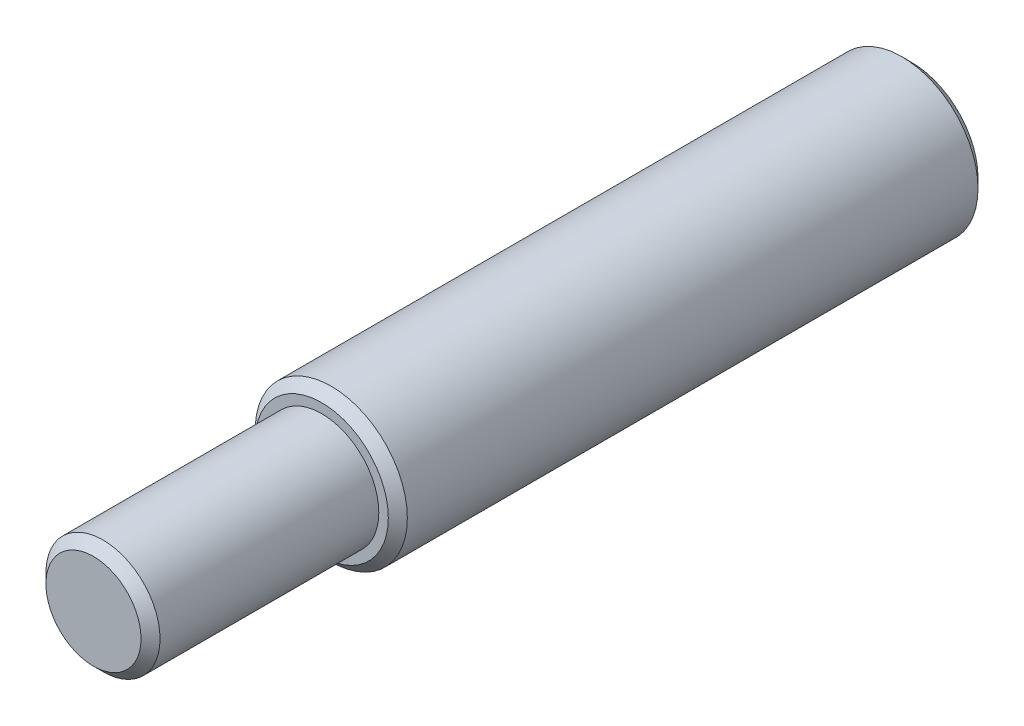
SolidWorks part; units mm, degrees
ref_plane "前视基准面" through (0, 0, 0) normal (0, 0, 1) x (1, 0, 0)
ref_plane "上视基准面" through (0, 0, 0) normal (0, 1, 0) x (1, 0, 0)
ref_plane "右视基准面" through (0, 0, 0) normal (1, 0, 0) x (0, 0, -1)
sketch "草图1" plane through (0, 0, 0) normal (0, 0, 1) x (1, 0, 0)
  circle A0 centre (0, 0) radius 4
  dimension "D1" = 8
extrude "凸台-拉伸1" add sketch "草图1" along normal blind 10
sketch "草图2" plane through (0, 0, 10) normal (0, 0, 1) x (1, 0, 0)
  line L1 (10, 0) -> (5, 8.6603)
  line L2 (5, 8.6603) -> (-5, 8.6603)
  line L3 (-5, 8.6603) -> (-10, 0)
  line L4 (-10, 0) -> (-5, -8.6603)
  line L5 (-5, -8.6603) -> (5, -8.6603)
  line L6 (5, -8.6603) -> (10, 0)
  circle A0 centre (0, 0) radius 10 construction
  circle A1 centre (0, 0) radius 8.6603 construction
  dimension "D1" = 20
extrude "凸台-拉伸2" add sketch "草图2" along normal blind 8
sketch "草图3" plane through (0, 0, 18) normal (0, 0, 1) x (1, 0, 0)
  circle A0 centre (0, 0) radius 4
  dimension "D1" = 8
extrude "凸台-拉伸3" add sketch "草图3" along normal blind 13
sketch "草图4" plane through (0, 0, 31) normal (0, 0, 1) x (1, 0, 0)
  circle A0 centre (0, 0) radius 3
  dimension "D1" = 6
extrude "凸台-拉伸4" add sketch "草图4" along normal blind 12
chamfer "倒角1" distance 0.5 angle 45 3 edges at (3, 0, 43) (4, 0, 31) (4, 0, 0)
sketch "草图5" plane through (0, 0, 10) normal (0, 0, -1) x (-1, 0, 0)
  circle A0 centre (0, 0) radius 4
  circle A1 centre (0, 0) radius 13.0642
  dimension "D1" = 8
extrude "切除-拉伸1" cut sketch "草图5" against normal blind 10
